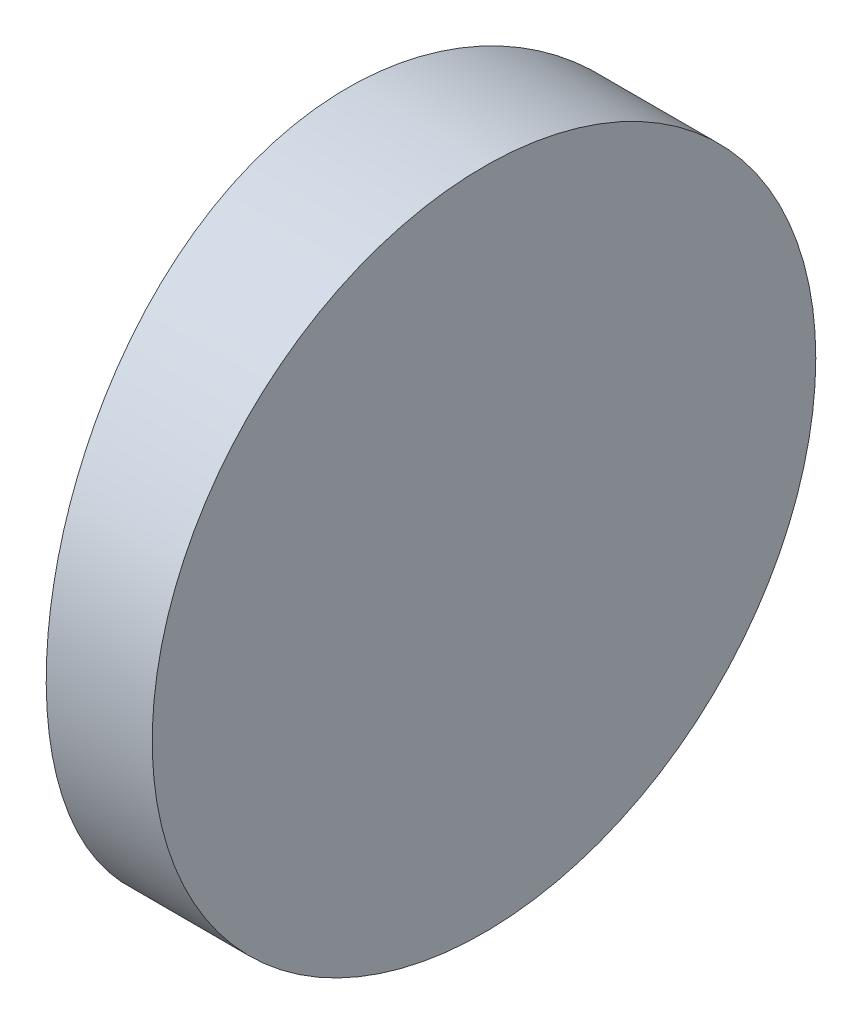
SolidWorks part; units mm, degrees
ref_plane "前视基准面" through (0, 0, 0) normal (0, 0, 1) x (1, 0, 0)
ref_plane "上视基准面" through (0, 0, 0) normal (0, 1, 0) x (1, 0, 0)
ref_plane "右视基准面" through (0, 0, 0) normal (1, 0, 0) x (0, 0, -1)
sketch "草图1" plane through (0, 0, 0) normal (0, 1, 0) x (1, 0, 0)
  line L0 (10.7432, 0) -> (-20.3908, 0) construction
  line L1 (-29.4519, 6.25) -> (-27.4548, 6.25)
  line L2 (-29.4519, -6.25) -> (-27.4548, -6.25)
  line L3 (-27.4548, 6.25) -> (-27.4548, -6.25)
  arc A0 (-29.4519, 6.25) -> (-29.4519, -6.25) centre (4.3552, 0) ccw
  point P19 (-30.0248, 0)
  point P20 (-27.4548, 0)
  dimension "D2" = 6.25
  dimension "D3" = 34.38
  dimension "D4" = 2.57
  dimension "D1" = 6.25
extrude "凸台-拉伸1" add sketch "草图1" along normal blind 12.5 contours A0 L2 L3 L1
sketch "草图2" plane through (-27.4548, 0, 0) normal (1, 0, 0) x (0, 0, -1)
  line L0 (6.25, 0) -> (-6.25, 0) construction
  line L7 (-6.25, 0) -> (6.25, 0)
  line L8 (6.25, 0) -> (6.25, 12.5)
  line L9 (6.25, 12.5) -> (-6.25, 12.5)
  line L10 (-6.25, 12.5) -> (-6.25, 0)
  line L11 (-6.25, 0) -> (6.25, 0)
  line L12 (6.25, 0) -> (6.25, 12.5)
  line L13 (6.25, 12.5) -> (-6.25, 12.5)
  line L14 (-6.25, 12.5) -> (-6.25, 0)
  circle A0 centre (0, 6.25) radius 6.25
  line M1 (-6.25, 0) -> (6.25, 0)
  line M2 (6.25, 0) -> (6.25, 12.5)
  line M3 (6.25, 12.5) -> (-6.25, 12.5)
  line M4 (-6.25, 12.5) -> (-6.25, 0)
  dimension "D1" = 12.5
  dimension "D2" = 6.25
  dimension "D3" = 0
extrude "切除-拉伸8" cut sketch "草图2" against normal blind 12.7 contours A0 L13 M4 | A0 L12 M3 | A0 L11 M2 | A0 L14 M1
